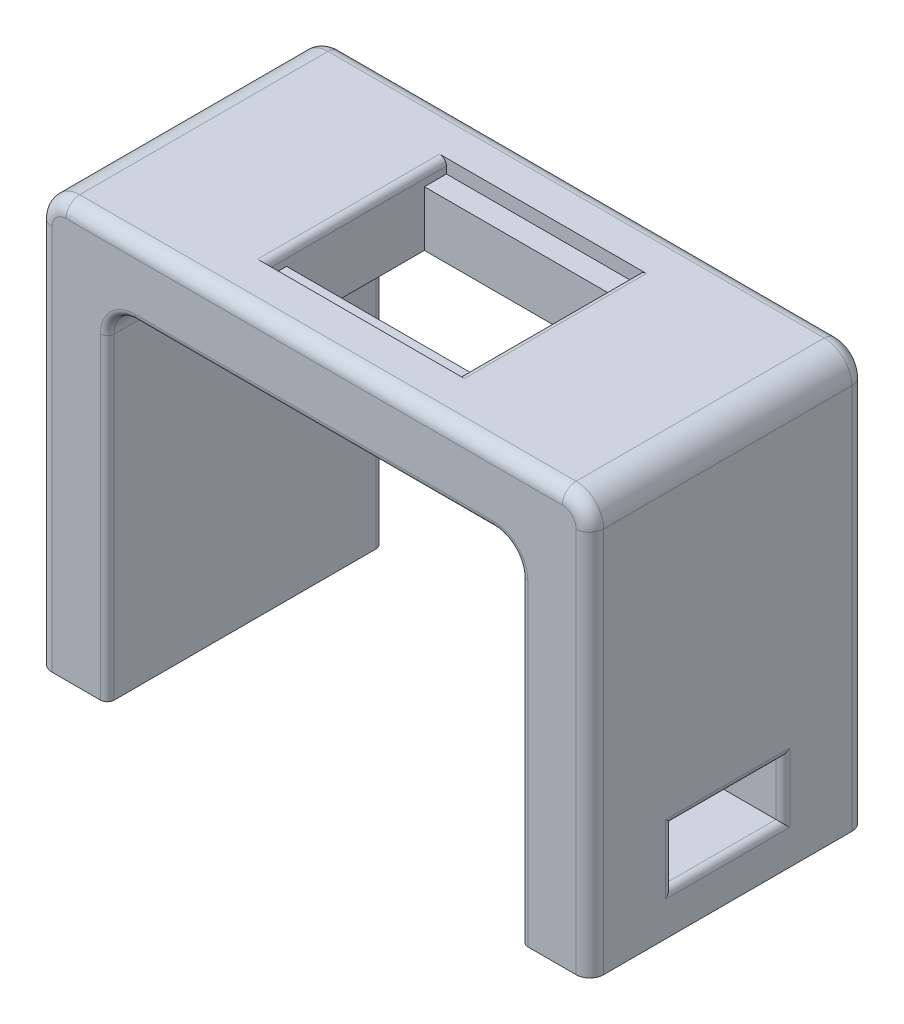
SolidWorks part; units mm, degrees
ref_plane "Front Plane" through (0, 0, 0) normal (0, 0, 1) x (1, 0, 0)
ref_plane "Top Plane" through (0, 0, 0) normal (0, 1, 0) x (1, 0, 0)
ref_plane "Right Plane" through (0, 0, 0) normal (1, 0, 0) x (0, 0, -1)
sketch "Sketch1" plane through (0, 0, 0) normal (0, 0, 1) x (1, 0, 0)
  line L0 (0, 0) -> (0, 76.2)
  line L1 (0, 76.2) -> (101.6, 76.2)
  line L2 (101.6, 76.2) -> (101.6, 0)
  line L3 (101.6, 0) -> (88.9, 0)
  line L4 (88.9, 0) -> (88.9, 63.5)
  line L5 (88.9, 63.5) -> (12.7, 63.5)
  line L6 (12.7, 63.5) -> (12.7, 0)
  line L7 (12.7, 0) -> (0, 0)
  dimension "D1" = 12.7
  dimension "D2" = 12.7
  dimension "D3" = 12.7
  dimension "D4" = 76.2
  dimension "D5" = 101.6
extrude "Boss-Extrude1" add sketch "Sketch1" along normal blind 50.8
fillet "Fillet1" radius 5.08 4 edges at (88.9, 63.5, 25.4) (12.7, 63.5, 25.4) (101.6, 76.2, 25.4) (0, 76.2, 25.4)
sketch "Sketch2" plane through (0, 76.2, 0) normal (0, 1, 0) x (1, 0, 0)
  line L0 (5.08, -25.4) -> (96.52, -25.4) construction
  line L1 (5.08, 0) -> (5.08, -50.8) construction
  line L2 (96.52, -50.8) -> (96.52, 0) construction
  line L3 (50.8, 0) -> (50.8, -50.8) construction
  line L4 (96.52, 0) -> (5.08, 0) construction
  line L5 (96.52, -50.8) -> (5.08, -50.8) construction
  line L6 (68.58, -8.636) -> (33.02, -8.636)
  line L7 (33.02, -8.636) -> (33.02, -42.164)
  line L8 (68.58, -8.636) -> (68.58, -42.164)
  line L9 (68.58, -42.164) -> (33.02, -42.164)
  point P16 (50.8, -8.636)
  point P18 (68.58, -25.4)
  point P19 (33.02, -25.4)
  dimension "D1" = 17.78
  dimension "D2" = 16.764
extrude "Cut-Extrude1" cut sketch "Sketch2" against normal blind 2.54
sketch "Sketch4" plane through (0, 73.66, 0) normal (0, 1, 0) x (1, 0, 0)
  line L0 (33.02, -12.7) -> (68.58, -12.7)
  line L1 (33.02, -8.636) -> (33.02, -42.164) construction
  line L2 (68.58, -42.164) -> (68.58, -8.636) construction
  line L3 (33.02, -25.4) -> (68.58, -25.4) construction
  line L4 (33.02, -8.636) -> (33.02, -42.164) construction
  line L5 (68.58, -42.164) -> (68.58, -8.636) construction
  line L6 (33.02, -38.1) -> (33.02, -12.7)
  line L7 (68.58, -12.7) -> (68.58, -38.1)
  line L9 (33.02, -38.1) -> (68.58, -38.1)
  dimension "D1" = 25.4
extrude "Cut-Extrude2" cut sketch "Sketch4" against normal through all
fillet "Fillet2" radius 1.27 2 edges at (68.58, 76.2, 25.4) (33.02, 76.2, 25.4)
sketch "Sketch6" plane through (101.6, 0, 0) normal (1, 0, 0) x (0, 0, -1)
  line L0 (-50.8, 12.7) -> (0, 12.7) construction
  line L1 (-50.8, 0) -> (-50.8, 71.12) construction
  line L2 (0, 0) -> (0, 71.12) construction
  line L3 (-50.8, 0) -> (-50.8, 12.7)
  line L4 (-25.4, 0) -> (-25.4, 25.9876) construction
  line L6 (-50.8, 0) -> (0, 0) construction
  line L7 (-35.56, 7.62) -> (-35.56, 17.78)
  line L8 (-35.56, 17.78) -> (-15.24, 17.78)
  line L9 (-15.24, 7.62) -> (-15.24, 17.78)
  line L10 (-35.56, 7.62) -> (-15.24, 7.62)
  point P17 (-25.4, 17.78)
  point P18 (-35.56, 12.7)
  point P19 (-15.24, 12.7)
  dimension "D2" = 10.16
  dimension "D3" = 5.08
  dimension "D1" = 12.7
extrude "Cut-Extrude3" cut sketch "Sketch6" against normal up to next contours L7 L10 L9 L8
fillet "Fillet3" radius 2.54 10 edges at (0, 35.56, 0) (1.4879, 74.7121, 0) (50.8, 76.2, 0) (100.1121, 74.7121, 0) (101.6, 35.56, 50.8) (100.1121, 74.7121, 50.8) (50.8, 76.2, 50.8) (1.4879, 74.7121, 50.8) (101.6, 35.56, 0) (0, 35.56, 50.8)
fillet "Fillet4" radius 1.27 4 edges at (101.6, 12.7, 15.24) (101.6, 17.78, 25.4) (101.6, 12.7, 35.56) (101.6, 7.62, 25.4)
fillet "Fillet5" radius 1.27 10 edges at (12.7, 29.21, 0) (14.1879, 62.0121, 0) (50.8, 63.5, 0) (87.4121, 62.0121, 0) (88.9, 29.21, 50.8) (87.4121, 62.0121, 50.8) (50.8, 63.5, 50.8) (14.1879, 62.0121, 50.8) (88.9, 29.21, 0) (12.7, 29.21, 50.8)
